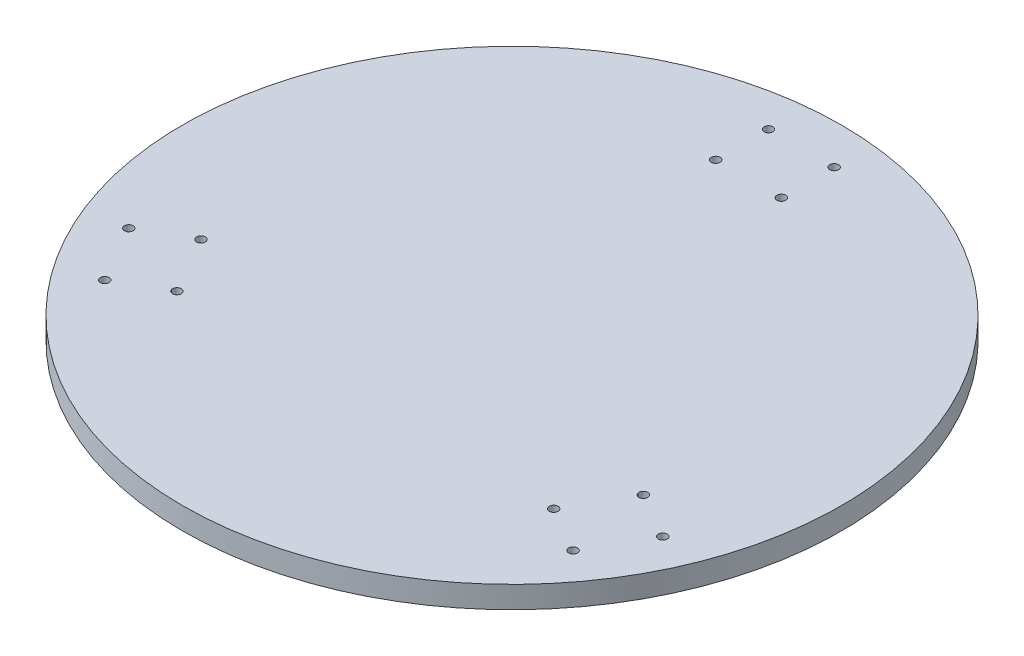
SolidWorks part; units mm, degrees
material "Acrylic"
ref_plane "Front Plane" through (0, 0, 0) normal (0, 0, 1) x (1, 0, 0)
ref_plane "Top Plane" through (0, 0, 0) normal (0, 1, 0) x (1, 0, 0)
ref_plane "Right Plane" through (0, 0, 0) normal (1, 0, 0) x (0, 0, -1)
sketch "Sketch1" plane through (0, 0, 0) normal (0, 1, 0) x (1, 0, 0)
  circle A0 centre (0, 0) radius 150
extrude "Boss-Extrude1" add sketch "Sketch1" along normal blind 10
sketch "Sketch2" plane through (0, 10, 0) normal (0, 1, 0) x (1, 0, 0)
  line L0 (0, 0) -> (-177.8464, 0) construction
  line L1 (0, 0) -> (0, 145.1898) construction
  line L2 (0, 0) -> (115.5258, 115.5258) construction
  circle A0 centre (-14.945, 131.7064) radius 2
  circle A1 centre (-14.945, 107.6464) radius 2
  circle A2 centre (14.945, 107.6464) radius 2
  circle A3 centre (14.945, 131.7064) radius 2
  circle A4 centre (85.7521, -66.766) radius 2
  circle A5 centre (100.6971, -40.8805) radius 2
  circle A6 centre (106.5886, -78.796) radius 2
  circle A7 centre (121.5336, -52.9105) radius 2
  circle A8 centre (-100.6971, -40.8805) radius 2
  circle A9 centre (-85.7521, -66.766) radius 2
  circle A10 centre (-121.5336, -52.9105) radius 2
  circle A11 centre (-106.5886, -78.796) radius 2
  point P32 (0, 0)
  dimension "D1" = 14.945
  dimension "D2" = 4
  dimension "D3" = 24.06
  dimension "D4" = 3
extrude "Cut-Extrude1" cut sketch "Sketch2" against normal blind 10
